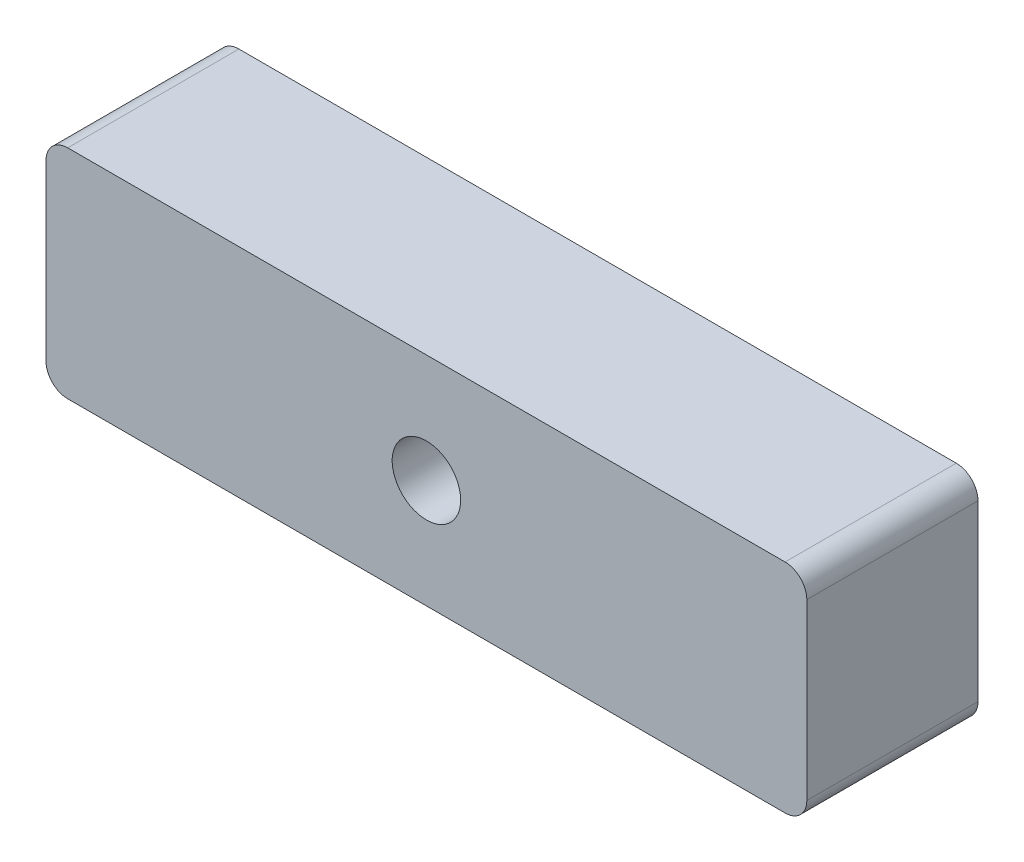
SolidWorks part; units mm, degrees
material "Balsa"
ref_plane "Front Plane" through (0, 0, 0) normal (0, 0, 1) x (1, 0, 0)
ref_plane "Top Plane" through (0, 0, 0) normal (0, 1, 0) x (1, 0, 0)
ref_plane "Right Plane" through (0, 0, 0) normal (1, 0, 0) x (0, 0, -1)
sketch "Sketch2" plane through (0, 0, 0) normal (0, 0, 1) x (1, 0, 0)
  line L1 (-41.91, -12.7) -> (41.91, -12.7)
  line L2 (-44.45, -10.16) -> (-44.45, 10.16)
  line L3 (-41.91, 12.7) -> (41.91, 12.7)
  line L4 (44.45, -10.16) -> (44.45, 10.16)
  line L5 (-44.45, -12.7) -> (44.45, 12.7) construction
  line L6 (-44.45, 12.7) -> (44.45, -12.7) construction
  arc A0 (41.91, 12.7) -> (44.45, 10.16) centre (41.91, 10.16) cw
  arc A1 (41.91, -12.7) -> (44.45, -10.16) centre (41.91, -10.16) ccw
  arc A2 (-41.91, -12.7) -> (-44.45, -10.16) centre (-41.91, -10.16) cw
  arc A3 (-44.45, 10.16) -> (-41.91, 12.7) centre (-41.91, 10.16) cw
  point P0 (0, 0)
  dimension "D3" = 2.54
  dimension "D1" = 25.4
  dimension "D2" = 88.9
extrude "Boss-Extrude1" add sketch "Sketch2" along normal blind 20 contours A3 L2 A2 L1 A1 L4 A0 L3
sketch "Sketch3" plane through (0, 0, 20) normal (0, 0, 1) x (1, 0, 0)
  circle A0 centre (0, 0) radius 4
  dimension "D1" = 8
extrude "Cut-Extrude1" cut sketch "Sketch3" against normal blind 20 contours A0
